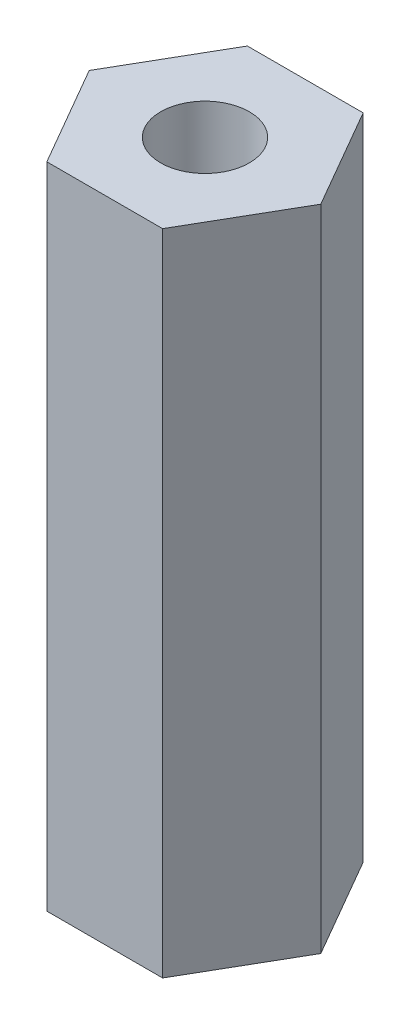
SolidWorks part; units mm, degrees
material "Brass"
ref_plane "Front Plane" through (0, 0, 0) normal (0, 0, 1) x (1, 0, 0)
ref_plane "Top Plane" through (0, 0, 0) normal (0, 1, 0) x (1, 0, 0)
ref_plane "Right Plane" through (0, 0, 0) normal (1, 0, 0) x (0, 0, -1)
sketch "Sketch1" plane through (0, 0, 0) normal (0, 1, 0) x (1, 0, 0)
  line L1 (1.3382, -2.3178) -> (2.6763, 0)
  line L2 (2.6763, 0) -> (1.3382, 2.3177)
  line L3 (1.3382, 2.3177) -> (-1.3382, 2.3178)
  line L4 (-1.3382, 2.3178) -> (-2.6763, 0)
  line L5 (-2.6763, 0) -> (-1.3382, -2.3177)
  line L6 (-1.3382, -2.3177) -> (1.3382, -2.3178)
  circle A0 centre (0, 0) radius 2.3178 construction
  dimension "D1" = 4.6355
extrude "Boss-Extrude1" add sketch "Sketch1" along normal blind 15
hole_wizard "M2.5x0.45 Tapped Hole1" positions "Sketch2" profile "Sketch3" tap size "M2.5x0.45" standard "ANSI Metric"
sketch "Sketch2" plane through (0, 0, 0) normal (0, -1, 0) x (-1, 0, 0)
  point P0 (0, 0)
sketch "Sketch3" plane through (0, 0, 0) normal (1, 0, 0) x (0, 0, -1)
  line L0 (0, 0) -> (0, 42.6159)
  line L1 (0, 42.6159) -> (1.025, 42)
  line L2 (1.025, 42) -> (1.025, 0)
  line L5 (1.025, 0) -> (0, 0)
  line L10 (0, 42.6159) -> (-1.025, 42) construction
  line L11 (0, -6.35) -> (0, 107.95) construction
  dimension "Tap Drill Dia." = 2.05
  dimension "Tap Drill Depth" = 42
  dimension "Drill Angle" = 118
